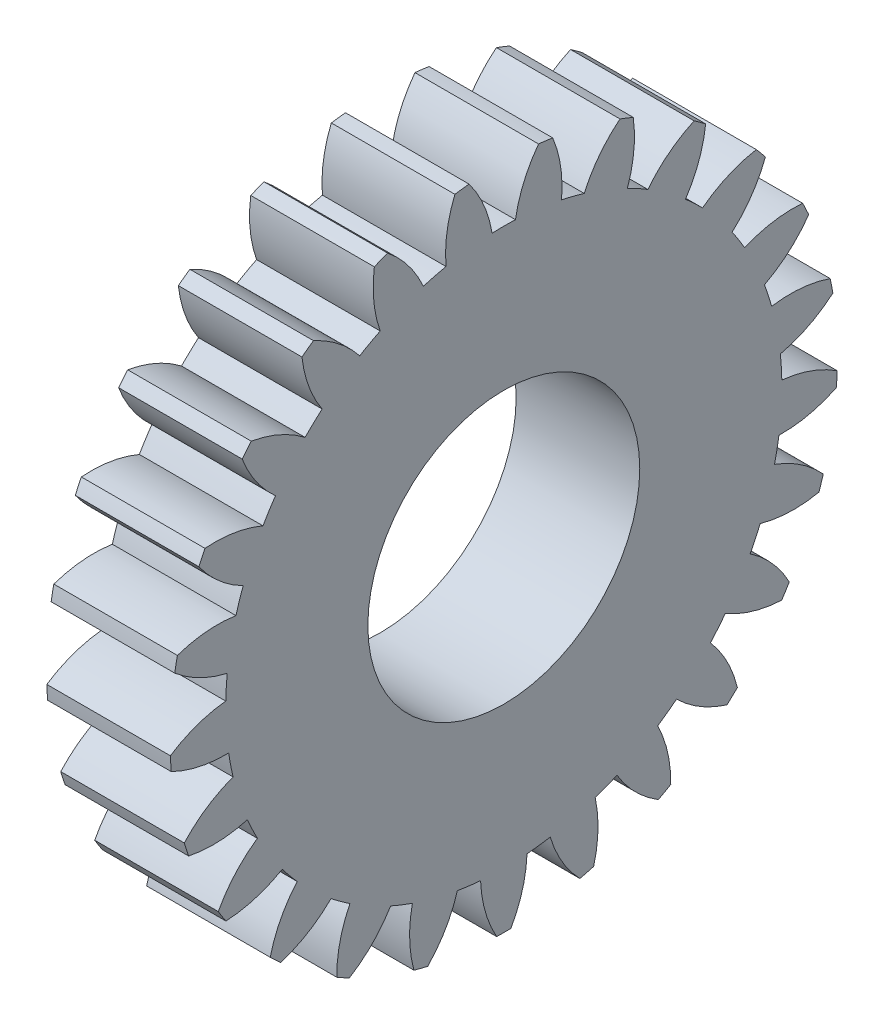
SolidWorks part; units mm, degrees
ref_plane "Plane1" through (0, 0, 0) normal (0, 0, 1) x (1, 0, 0)
ref_plane "Plane2" through (0, 0, 0) normal (0, 1, 0) x (1, 0, 0)
ref_plane "Plane3" through (0, 0, 0) normal (1, 0, 0) x (0, 0, -1)
sketch "HoldingSke" plane through (0, 0, 0) normal (0, 1, 0) x (1, 0, 0)
  line L0 (0, 0) -> (0.4532, -0.2113)
  line L1 (-15, 0) -> (100, 0) construction
  line L2 (0, 0) -> (-2.1039, 2.3779)
  line L3 (0, 0) -> (-11.863, 4.5341)
  line L4 (0, 0) -> (7.8269, 3.6497)
  line L5 (0, 0) -> (-46.8476, -17.4728)
  line L6 (0, 0) -> (-8.2896, -5.593)
  line L7 (-2.1039, 2.3779) -> (8.6586, 51.2059)
  line L8 (-76.2, 54.61) -> (-72.9, 54.61)
  line L9 (-71.009, 38.7566) -> (-53.1078, 45.2721)
  line L10 (-76.2, 71.12) -> (104.1128, 71.12)
  line L11 (0, 0) -> (-10, 0)
  line L12 (-76.2, 101.6) -> (-76.133, 101.6)
  line L13 (24.9733, 27.94) -> (52.9518, 28.4284)
  line L14 (24.9733, 27.94) -> (24.9743, 27.94)
  line L15 (24.9733, 27.94) -> (100.4006, 29.5858)
  line L16 (-63.627, -2) -> (-12.827, -2)
  circle A0 centre (0, 0) radius 11
  circle A1 centre (0, 0) radius 22.499
  circle A2 centre (0, 0) radius 37.5
  circle A3 centre (0, 0) radius 11
  dimension "MHD" = 44.998
  dimension "Hub_dia" = 75
  dimension "Bore" = 22
  dimension "MBD" = 22
  dimension "Num_teeth" = 25
  dimension "Pitch" = 0.5
  dimension "Overall_len" = 50
  dimension "Show_teeth" = 25
  dimension "Thickness" = 10
  dimension "OAL" = 50.0001
  dimension "T_dim" = 3.3
  dimension "Ap" = 20
  dimension "H" = 19.05
  dimension "Pitch_radius" = 180.3128
  dimension "Width" = 10
  dimension "Backlash" = 0.067
  dimension "Addendum_fac" = 1
  dimension "Dedendum_fac" = 1.25
  dimension "Clearance_fac" = 0.25
  dimension "Dedendum_add" = 0.001
  dimension "Module" = 2
sketch "BasProSke" plane through (0, 0, 0) normal (0, 1, 0) x (1, 0, 0)
  line L0 (-10, 0) -> (60, 0) construction
  line L1 (0, 0) -> (0, 27)
  line L2 (0, 0) -> (10, 0)
  line L3 (10, 0) -> (10, 27)
  line L4 (10, 27) -> (0, 27)
  dimension "Thickness" = 10
  dimension "Diameter" = 54
revolve "Base-Revolve" add sketch "BasProSke" angle 360 about L0
sketch "TooCutSke" plane through (0, 0, 0) normal (1, 0, 0) x (0, 0, -1)
  line L1 (0, 0) -> (0, 107) construction
  line L2 (0, 0) -> (-1.687, 24.943) construction
  line L3 (0, 0) -> (-6.2561, 49.5219) construction
  line L4 (-1.687, 24.943) -> (-3.128, 24.761) construction
  arc A0 (0.9462, 22.4791) -> (-0.9462, 22.4791) centre (0, 0) ccw
  arc A1 (2.8295, 26.8769) -> (-2.8295, 26.8769) centre (0, 0) ccw
  circle A2 centre (0, 0) radius 25 construction
  circle A3 centre (0, 0) radius 23.4923 construction
  arc A4 (-0.9462, 22.4791) -> (-2.8295, 26.8769) centre (-10.8135, 20.8556) ccw
  arc A5 (2.8295, 26.8769) -> (0.9462, 22.4791) centre (10.8135, 20.8556) ccw
  dimension "Root_dia" = 44.998
  dimension "Overcut_dia" = 54.0508
  dimension "Pitch_dia" = 50
  dimension "Base_dia" = 46.9846
  dimension "Flank_rad" = 10
  dimension "Half_ang" = 7.2
  dimension "Half_CT" = 1.4525
extrude "ToothCut" cut sketch "TooCutSke" along normal through all
fillet "Breaks" [suppressed] radius 0.04
fillet "RootFillets" [suppressed] radius 0.501
pattern_circular "TeethCuts" count 25 every 14.4 about axis through (-10, 0, 0) along (1, 0, 0) of "ToothCut", "RootFillets", "Breaks"
sketch "HubNeaOneSke" plane through (0, 0, 0) normal (-1, 0, 0) x (0, 0, 1)
  circle A0 centre (0, 0) radius 22.499
  dimension "Diameter" = 44.998
extrude "HubNearOne" [suppressed] add sketch "HubNeaOneSke" along normal blind 40.0001
sketch "HubNeaBotSke" plane through (0, 0, 0) normal (-1, 0, 0) x (0, 0, 1)
  circle A0 centre (0, 0) radius 22.499
  dimension "Diameter" = 44.998
extrude "HubNearBoth" [suppressed] add sketch "HubNeaBotSke" along normal blind 20
ref_plane "FarPln" through (10, 0, 0) normal (1, 0, 0) x (0, 0, -1)
sketch "HubFarSke" plane through (10, 0, 0) normal (1, 0, 0) x (0, 0, -1)
  circle A0 centre (0, 0) radius 22.499
  dimension "Diameter" = 44.998
extrude "HubFar" [suppressed] add sketch "HubFarSke" along normal blind 20
sketch "BorSke" plane through (0, 0, 0) normal (1, 0, 0) x (0, 0, -1)
  circle A0 centre (0, 0) radius 11
  dimension "Diameter" = 22
extrude "Bore" cut sketch "BorSke" along normal mid plane 100.0001
sketch "KeySke" plane through (0, 0, 0) normal (1, 0, 0) x (0, 0, -1)
  line L0 (-4, 0) -> (-4, 14.3)
  line L1 (-4, 14.3) -> (4, 14.3)
  line L2 (4, 14.3) -> (4, 0)
  line L3 (0, 0) -> (0, 34) construction
  line L4 (-4, 0) -> (4, 0)
  dimension "Offset" = 14.3
  dimension "Width" = 8
extrude "Keyway" [suppressed] cut sketch "KeySke" along normal mid plane 100.0001
pattern_circular "Keyway2" [suppressed] count 2 every 90 about axis through (-10, 0, 0) along (1, 0, 0)
equation "' \"Module@HoldingSke\" = 6.35"
equation "' \"Num_teeth@HoldingSke\" = 12"
equation "' \"Ap@HoldingSke\" =  20"
equation "' \"Ap@HoldingSke\" = 20"
equation "' \"Width@HoldingSke\" = 0.5 * 25.4"
equation "' \"Hub_dia@HoldingSke\"= 1 * 25.4"
equation "' \"Hub_dia@HoldingSke\" = 1 * 25.4"
equation "' \"Overall_len@HoldingSke\" = 1.0 * 25.4"
equation "' \"Bore@HoldingSke\" = 0.75 * 25.4"
equation "' \"T_dim@HoldingSke\" = 0.1 * 25.4"
equation "' \"Width@KeySke\" = 0.25 * 25.4"
equation "' \"Show_teeth@HoldingSke\" = 13"
equation "' \"Backlash@HoldingSke\" = 0.009 * 25.4"
equation "' \"Addendum_fac@HoldingSke\" = 1.0"
equation "' \"Dedendum_fac@HoldingSke\" = 1.25"
equation "' \"Dedendum_add@HoldingSke\" = 0.00005 * 25.4"
equation "' \"Clearance_fac@HoldingSke\" = 0.25"
equation "\"Pitch@HoldingSke\" = 1 / \"Module@HoldingSke\""
equation "\"Overcut_dia@TooCutSke\" = (\"Num_teeth@HoldingSke\" + 2 * \"Addendum_fac@HoldingSke\") / \"Pitch@HoldingSke\" + 0.002 * 25.4"
equation "\"Pitch_dia@TooCutSke\" = \"Num_teeth@HoldingSke\" / \"Pitch@HoldingSke\""
equation "\"Base_dia@TooCutSke\" = \"Num_teeth@HoldingSke\" / \"Pitch@HoldingSke\" * cos((\"Ap@HoldingSke\"  * 3.14159265 / 180))"
equation "\"Root_dia@TooCutSke\" = (\"Num_teeth@HoldingSke\" + 2) / \"Pitch@HoldingSke\" - 2 * (\"Addendum_fac@HoldingSke\" + \"Dedendum_fac@HoldingSke\") / \"Pitch@HoldingSke\" - \"Dedendum_add@HoldingSke\" * 2"
equation "\"Half_ang@TooCutSke\" = 180 / \"Num_teeth@HoldingSke\""
equation "\"Half_CT@TooCutSke\" = \"Num_teeth@HoldingSke\" / \"Pitch@HoldingSke\" * sin((3.14159265 / 2 / \"Num_teeth@HoldingSke\")) / 2 - 7 * \"Backlash@HoldingSke\" / 4"
equation "\"Flank_rad@TooCutSke\" = \"Num_teeth@HoldingSke\" / \"Pitch@HoldingSke\" / 5"
equation "\"Radius@RootFillets\" = \"Clearance_fac@HoldingSke\" / \"Pitch@HoldingSke\" + \"Dedendum_add@HoldingSke\""
equation "\"Break_rad@Breaks\" = 0.02 / \"Pitch@HoldingSke\""
equation "\"Thickness@HoldingSke\" = \"Width@HoldingSke\""
equation "\"OAL@HoldingSke\" = \"Thickness@HoldingSke\""
equation "\"MHD@HoldingSke\" = (\"Num_teeth@HoldingSke\" + 2) / \"Pitch@HoldingSke\" - 2 * (\"Addendum_fac@HoldingSke\" + \"Dedendum_fac@HoldingSke\")  / \"Pitch@HoldingSke\" - \"Dedendum_add@HoldingSke\" * 2"
equation "\"MBD@HoldingSke\" = (\"Num_teeth@HoldingSke\" + 2) / \"Pitch@HoldingSke\" - 2 * (\"Addendum_fac@HoldingSke\" + \"Dedendum_fac@HoldingSke\")  / \"Pitch@HoldingSke\" - \"Dedendum_add@HoldingSke\" * 2 - 0.002 * 25.4"
equation "\"MHD@HoldingSke\" = ((sgn( \"MHD@HoldingSke\" - \"Hub_dia@HoldingSke\" )-1)*( \"MHD@HoldingSke\" - \"Hub_dia@HoldingSke\" ))/-2+ \"Hub_dia@HoldingSke\""
equation "\"MBD@HoldingSke\" = ((sgn( \"MBD@HoldingSke\" - \"Bore@HoldingSke\" )-1)*( \"MBD@HoldingSke\" - \"Bore@HoldingSke\" ))/-2+ \"Bore@HoldingSke\""
equation "\"OAL@HoldingSke\" = ((sgn( \"OAL@HoldingSke\" - \"Overall_len@HoldingSke\" )+1)*( \"OAL@HoldingSke\" - \"Overall_len@HoldingSke\" ))/2 + \"Overall_len@HoldingSke\" + 0.000002 * 25.4"
equation "\"Num_teeth@TeethCuts\" = int( \"Show_teeth@HoldingSke\" ) + 1"
equation "\"Num_teeth@TeethCuts\" = ((sgn( \"Num_teeth@TeethCuts\" - \"Num_teeth@HoldingSke\" )-1)*( \"Num_teeth@TeethCuts\" - \"Num_teeth@HoldingSke\" ))/-2+ \"Num_teeth@HoldingSke\""
equation "\"Num_teeth@TeethCuts\" = ((sgn( \"Num_teeth@TeethCuts\" - 2.0)+1)*( \"Num_teeth@TeethCuts\" - 2.0))/2 +2.0"
equation "\"Angle@TeethCuts\" = 360.0 / \"Num_teeth@HoldingSke\""
equation "\"Diameter@BasProSke\" = (\"Num_teeth@HoldingSke\" + 2 * \"Addendum_fac@HoldingSke\") / \"Pitch@HoldingSke\""
equation "\"Thickness@BasProSke\"  = \"Thickness@HoldingSke\""
equation "' \"Fillet_rad@BasProSke\" =  \"Thickness@HoldingSke\" * 0.05"
equation "' \"Fillet_rad@BasProSke\" = \"Thickness@HoldingSke\" * 0.05"
equation "\"MHD@HoldingSke\" = ((sgn( \"MHD@HoldingSke\" - \"Root_dia@TooCutSke\" )-1)*( \"MHD@HoldingSke\" - \"Root_dia@TooCutSke\" ))/-2+ \"Root_dia@TooCutSke\""
equation "\"Diameter@HubNeaOneSke\" = \"MHD@HoldingSke\""
equation "\"Length@HubNearOne\" = \"OAL@HoldingSke\" - \"Thickness@BasProSke\""
equation "\"Diameter@HubNeaBotSke\" = \"MHD@HoldingSke\""
equation "\"Length@HubNearBoth\" = ( \"OAL@HoldingSke\" - \"Thickness@BasProSke\" ) / 2.0"
equation "\"Thickness@FarPln\" = \"Thickness@BasProSke\""
equation "\"Diameter@HubFarSke\" = \"MHD@HoldingSke\""
equation "\"Length@HubFar\" = ( \"OAL@HoldingSke\" - \"Thickness@BasProSke\" ) / 2.0"
equation "\"Diameter@BorSke\" = \"MBD@HoldingSke\""
equation "\"D1@Bore\" = \"OAL@HoldingSke\" * 2.0"
equation "\"D1@Keyway\" = \"OAL@HoldingSke\" * 2.0"
equation "\"Offset@KeySke\" = \"T_dim@HoldingSke\" + \"MBD@HoldingSke\" / 2.0"
